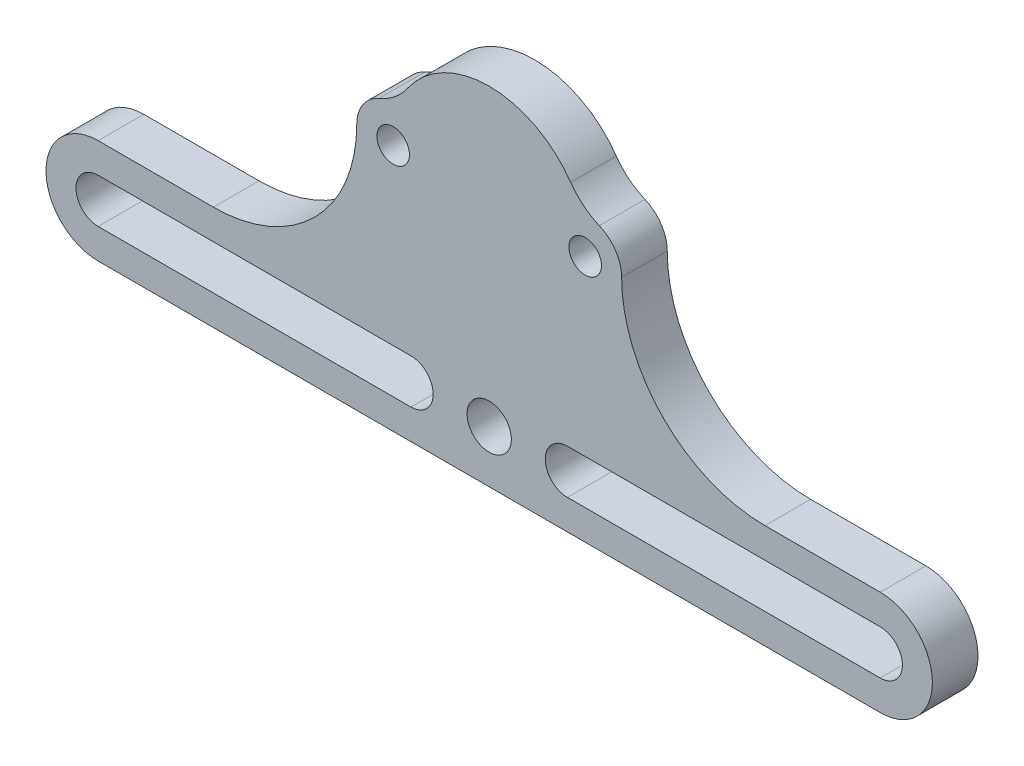
SolidWorks part; units mm, degrees
ref_plane "Front Plane" through (0, 0, 0) normal (0, 0, 1) x (1, 0, 0)
ref_plane "Top Plane" through (0, 0, 0) normal (0, 1, 0) x (1, 0, 0)
ref_plane "Right Plane" through (0, 0, 0) normal (1, 0, 0) x (0, 0, -1)
sketch "Sketch1" plane through (0, 0, 0) normal (0, 0, 1) x (1, 0, 0)
  line L0 (-30, -19) -> (30, -19)
  line L1 (30, -11) -> (21.16, -11)
  line L2 (-30, -11) -> (-21.16, -11)
  line L6 (-30, -15) -> (-6, -15) construction
  line L7 (-30, -13.3) -> (-6, -13.3)
  line L8 (-30, -16.7) -> (-6, -16.7)
  line L9 (30, -15) -> (6, -15) construction
  line L10 (30, -16.7) -> (6, -16.7)
  line L11 (30, -13.3) -> (6, -13.3)
  arc A0 (30, -19) -> (30, -11) centre (30, -15) ccw
  arc A1 (21.16, -11) -> (10.16, 0) centre (21.16, 0) cw
  arc A2 (-30, -19) -> (-30, -11) centre (-30, -15) cw
  arc A3 (-21.16, -11) -> (-10.16, 0) centre (-21.16, 0) ccw
  arc A7 (-30, -13.3) -> (-30, -16.7) centre (-30, -15) ccw
  arc A8 (8.4507, -2.5749) -> (8.4507, 2.5749) centre (7.366, 0) ccw
  arc A9 (6.2537, 4.3539) -> (8.4507, 2.5749) centre (10.4228, 7.2565) ccw
  arc A10 (6.2537, 4.3539) -> (-6.2537, 4.3539) centre (0, 0) ccw
  arc A11 (-8.4507, 2.5749) -> (-6.2537, 4.3539) centre (-10.4228, 7.2565) ccw
  arc A12 (-8.4507, 2.5749) -> (-8.4507, -2.5749) centre (-7.366, 0) ccw
  arc A13 (-6.2537, -4.3539) -> (-8.4507, -2.5749) centre (-10.4228, -7.2565) ccw
  arc A14 (-6.2537, -4.3539) -> (6.2537, -4.3539) centre (0, 0) ccw
  arc A15 (8.4507, -2.5749) -> (6.2537, -4.3539) centre (10.4228, -7.2565) ccw
  arc A16 (10.16, 0) -> (8.4507, 2.5749) centre (7.366, 0) ccw
  arc A17 (6.2537, 4.3539) -> (8.4507, 2.5749) centre (10.4228, 7.2565) ccw
  arc A18 (6.2537, 4.3539) -> (-6.2537, 4.3539) centre (0, 0) ccw
  arc A19 (-8.4507, 2.5749) -> (-6.2537, 4.3539) centre (-10.4228, 7.2565) ccw
  arc A20 (-8.4507, 2.5749) -> (-10.16, 0) centre (-7.366, 0) ccw
  arc A24 (-6, -16.7) -> (-6, -13.3) centre (-6, -15) ccw
  arc A25 (30, -16.7) -> (30, -13.3) centre (30, -15) ccw
  arc A26 (6, -13.3) -> (6, -16.7) centre (6, -15) ccw
  circle A42 centre (-7.366, 0) radius 1.25
  circle A43 centre (7.366, 0) radius 1.25
  circle A50 centre (0, -15) radius 1.7
  point P29 (0, -19)
  point P38 (-18, -15)
  point P44 (18, -15)
  dimension "D7" = 2.5
  dimension "D2" = 3.4
  dimension "D3" = 8
  dimension "D4" = 6
  dimension "D5" = 60
  dimension "D6" = 15
  dimension "D1" = 0
extrude "Boss-Extrude1" add sketch "Sketch1" along normal blind 3.5
